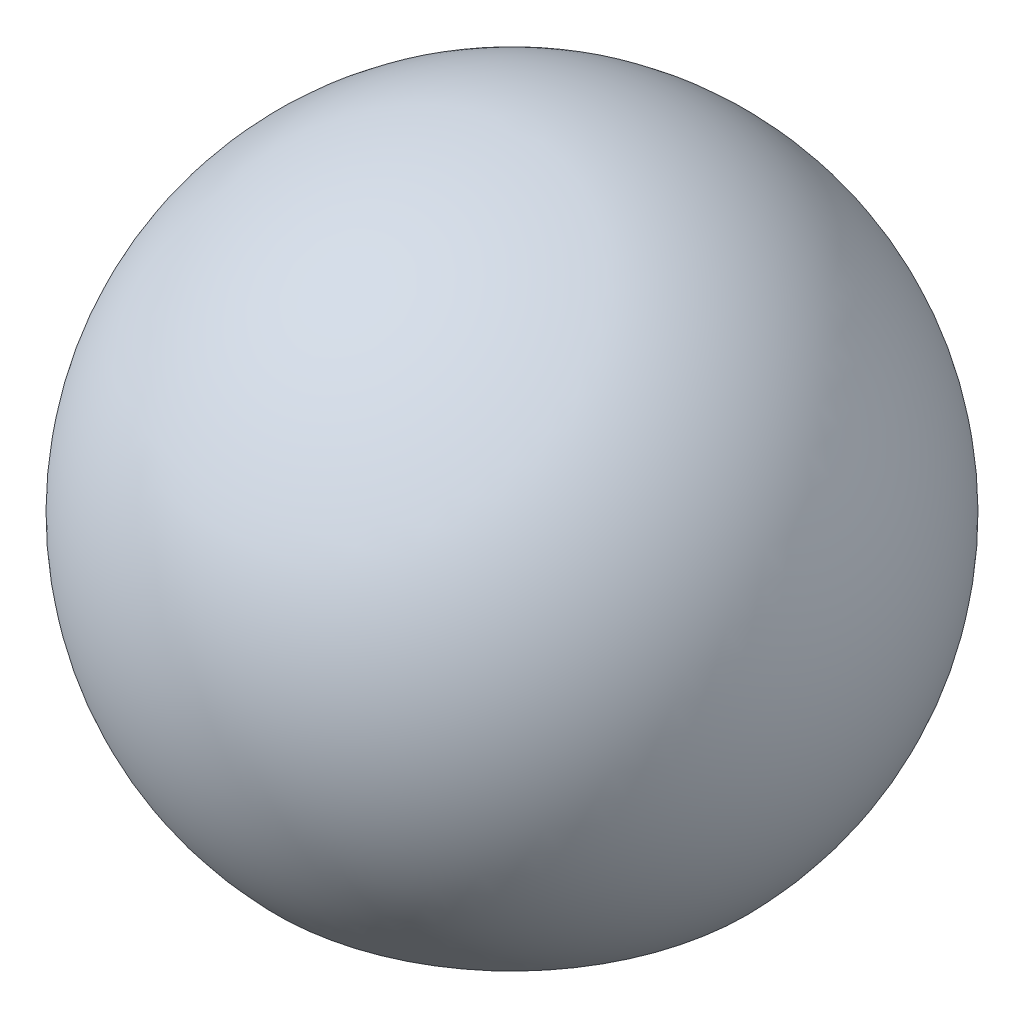
SolidWorks part; units mm, degrees
ref_plane "Front Plane" through (0, 0, 0) normal (0, 0, 1) x (1, 0, 0)
ref_plane "Top Plane" through (0, 0, 0) normal (0, 1, 0) x (1, 0, 0)
ref_plane "Right Plane" through (0, 0, 0) normal (1, 0, 0) x (0, 0, -1)
sketch "Sketch1" plane through (0, 0, 0) normal (0, 0, 1) x (1, 0, 0)
  line L0 (0, 0) -> (0, -3.7074) construction
  line L2 (0, -2.4495) -> (0, 3.5) construction
  line L3 (2.5, -2.4495) -> (0, -2.4495)
  line L4 (0, -2.4495) -> (0, 3.5)
  arc A0 (2.5, -2.4495) -> (0, 3.5) centre (0, 0) ccw
  point P7 (0, -2.4495)
  dimension "D1" = 7
  dimension "D2" = 2.5
revolve "Revolve2" add sketch "Sketch1" angle 360 about L4
